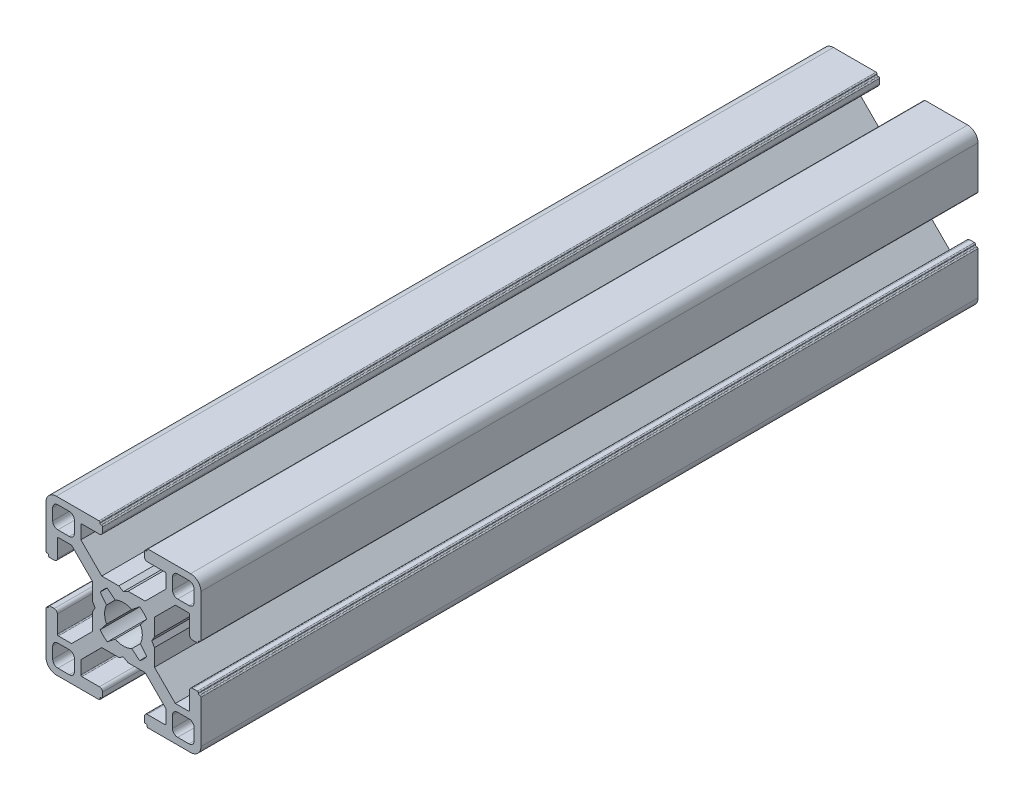
SolidWorks part; units mm, degrees
material "6061 Alloy"
ref_plane "Front" through (0, 0, 0) normal (0, 0, 1) x (1, 0, 0)
ref_plane "Top" through (0, 0, 0) normal (0, 1, 0) x (1, 0, 0)
ref_plane "Right" through (0, 0, 0) normal (1, 0, 0) x (0, 0, -1)
sketch "Sketch1" plane through (0, 0, 0) normal (0, 0, 1) x (1, 0, 0)
  line L0 (13.7, 12.7) -> (13.7, 10.5)
  line L1 (10.5, 9.5) -> (12.7, 9.5)
  line L2 (9.5, 12.7) -> (9.5, 10.5)
  line L3 (10.5, 13.7) -> (12.7, 13.7)
  line L4 (3.1359, 4.5184) -> (1.6001, 3.2806)
  line L5 (3.2806, 1.6001) -> (4.5053, 3.1547)
  line L6 (6.0045, 0.9) -> (5.4849, 0)
  line L7 (6.0045, 4.2045) -> (6.0045, 0.9)
  line L8 (0, -5.4849) -> (0.9, -6)
  line L9 (0.9, -6) -> (4.2045, -6)
  line L10 (4.2045, -6) -> (8.25, -10.05)
  line L11 (8.25, -10.05) -> (8.25, -12.6)
  line L12 (4.65, -12.8) -> (8.05, -12.8)
  line L13 (4.05, -14.3) -> (4.05, -13.4)
  line L14 (4.25, -14.5) -> (4.35, -14.5)
  line L15 (4.55, -14.8) -> (4.55, -14.7)
  line L16 (4.75, -15) -> (13, -15)
  line L17 (15, -13) -> (15, -4.75)
  line L18 (14.7, -4.55) -> (14.8, -4.55)
  line L19 (14.5, -4.35) -> (14.5, -4.25)
  line L20 (13.4, -4.05) -> (14.3, -4.05)
  line L21 (12.8, -8.05) -> (12.8, -4.65)
  line L22 (12.6, -8.25) -> (10.05, -8.25)
  line L23 (10.05, -8.25) -> (6.0045, -4.2045)
  line L24 (6.0045, -4.2045) -> (6.0045, -0.9)
  line L25 (6.0045, -0.9) -> (5.4849, 0)
  line L26 (10.05, 8.25) -> (6.0045, 4.2045)
  line L27 (12.6, 8.25) -> (10.05, 8.25)
  line L28 (12.8, 8.05) -> (12.8, 4.65)
  line L29 (13.4, 4.05) -> (14.3, 4.05)
  line L30 (14.5, 4.35) -> (14.5, 4.25)
  line L31 (14.7, 4.55) -> (14.8, 4.55)
  line L32 (15, 13) -> (15, 4.75)
  line L33 (4.75, 15) -> (13, 15)
  line L34 (4.55, 14.8) -> (4.55, 14.7)
  line L35 (4.25, 14.5) -> (4.35, 14.5)
  line L36 (4.05, 14.3) -> (4.05, 13.4)
  line L37 (4.65, 12.8) -> (8.05, 12.8)
  line L38 (8.25, 10.05) -> (8.25, 12.6)
  line L39 (4.2045, 6) -> (8.25, 10.05)
  line L40 (0.9, 6) -> (4.2045, 6)
  line L41 (0, 5.4849) -> (0.9, 6)
  line L42 (-13.7, -12.7) -> (-13.7, -10.5)
  line L43 (-10.5, -9.5) -> (-12.7, -9.5)
  line L44 (-9.5, -12.7) -> (-9.5, -10.5)
  line L45 (-10.5, -13.7) -> (-12.7, -13.7)
  line L46 (-3.1359, -4.5184) -> (-1.6001, -3.2806)
  line L47 (-3.2806, -1.6001) -> (-4.5053, -3.1547)
  line L48 (0, 5.4849) -> (-0.9, 6)
  line L49 (-0.9, 6) -> (-4.2045, 6)
  line L50 (-4.2045, 6) -> (-8.25, 10.05)
  line L51 (-8.25, 10.05) -> (-8.25, 12.6)
  line L52 (-4.65, 12.8) -> (-8.05, 12.8)
  line L53 (-4.05, 14.3) -> (-4.05, 13.4)
  line L54 (-4.25, 14.5) -> (-4.35, 14.5)
  line L55 (-4.55, 14.8) -> (-4.55, 14.7)
  line L56 (-4.75, 15) -> (-13, 15)
  line L57 (-15, 13) -> (-15, 4.75)
  line L58 (-14.7, 4.55) -> (-14.8, 4.55)
  line L59 (-14.5, 4.35) -> (-14.5, 4.25)
  line L60 (-13.4, 4.05) -> (-14.3, 4.05)
  line L61 (-12.8, 8.05) -> (-12.8, 4.65)
  line L62 (-12.6, 8.25) -> (-10.05, 8.25)
  line L63 (-10.05, 8.25) -> (-6.0045, 4.2045)
  line L64 (-6.0045, -0.9) -> (-5.4849, 0)
  line L65 (-6.0045, -4.2045) -> (-6.0045, -0.9)
  line L66 (-10.05, -8.25) -> (-6.0045, -4.2045)
  line L67 (-12.6, -8.25) -> (-10.05, -8.25)
  line L68 (-12.8, -8.05) -> (-12.8, -4.65)
  line L69 (-13.4, -4.05) -> (-14.3, -4.05)
  line L70 (-14.5, -4.35) -> (-14.5, -4.25)
  line L71 (-14.7, -4.55) -> (-14.8, -4.55)
  line L72 (-15, -13) -> (-15, -4.75)
  line L73 (-4.75, -15) -> (-13, -15)
  line L74 (-4.55, -14.8) -> (-4.55, -14.7)
  line L75 (-4.25, -14.5) -> (-4.35, -14.5)
  line L76 (-4.05, -14.3) -> (-4.05, -13.4)
  line L77 (3.2806, -1.6001) -> (4.5053, -3.1547)
  line L78 (3.1359, -4.5184) -> (1.6001, -3.2806)
  line L79 (-4.65, -12.8) -> (-8.05, -12.8)
  line L80 (-8.25, -10.05) -> (-8.25, -12.6)
  line L81 (-4.2045, -6) -> (-8.25, -10.05)
  line L82 (-0.9, -6) -> (-4.2045, -6)
  line L83 (0, -5.4849) -> (-0.9, -6)
  line L84 (10.5, -13.7) -> (12.7, -13.7)
  line L85 (9.5, -12.7) -> (9.5, -10.5)
  line L86 (10.5, -9.5) -> (12.7, -9.5)
  line L87 (13.7, -12.7) -> (13.7, -10.5)
  line L88 (-6.0045, 4.2045) -> (-6.0045, 0.9)
  line L89 (-6.0045, 0.9) -> (-5.4849, 0)
  line L90 (-3.2806, 1.6001) -> (-4.5053, 3.1547)
  line L91 (-3.1359, 4.5184) -> (-1.6001, 3.2806)
  line L92 (-10.5, 13.7) -> (-12.7, 13.7)
  line L93 (-9.5, 12.7) -> (-9.5, 10.5)
  line L94 (-10.5, 9.5) -> (-12.7, 9.5)
  line L95 (-13.7, 12.7) -> (-13.7, 10.5)
  line L96 (-23.4857, 0) -> (20.9308, 0) construction
  line L97 (0, 17.9563) -> (0, -17.361) construction
  arc A0 (13.7, 12.7) -> (12.7, 13.7) centre (12.7, 12.7) ccw
  arc A1 (12.7, 9.5) -> (13.7, 10.5) centre (12.7, 10.5) ccw
  arc A2 (9.5, 10.5) -> (10.5, 9.5) centre (10.5, 10.5) ccw
  arc A3 (10.5, 13.7) -> (9.5, 12.7) centre (10.5, 12.7) ccw
  arc A4 (1.6001, 3.2806) -> (-1.6001, 3.2806) centre (0, 0) ccw
  arc A5 (8.25, -12.6) -> (8.05, -12.8) centre (8.05, -12.6) cw
  arc A6 (4.65, -12.8) -> (4.05, -13.4) centre (4.65, -13.4) ccw
  arc A7 (4.05, -14.3) -> (4.25, -14.5) centre (4.25, -14.3) ccw
  arc A8 (4.35, -14.5) -> (4.55, -14.7) centre (4.35, -14.7) cw
  arc A9 (4.55, -14.8) -> (4.75, -15) centre (4.75, -14.8) ccw
  arc A10 (13, -15) -> (15, -13) centre (13, -13) ccw
  arc A11 (15, -4.75) -> (14.8, -4.55) centre (14.8, -4.75) ccw
  arc A12 (14.7, -4.55) -> (14.5, -4.35) centre (14.7, -4.35) cw
  arc A13 (14.5, -4.25) -> (14.3, -4.05) centre (14.3, -4.25) ccw
  arc A14 (13.4, -4.05) -> (12.8, -4.65) centre (13.4, -4.65) ccw
  arc A15 (12.8, -8.05) -> (12.6, -8.25) centre (12.6, -8.05) cw
  arc A16 (4.5053, 3.1547) -> (3.1359, 4.5184) centre (0, 0) ccw
  arc A17 (12.8, 8.05) -> (12.6, 8.25) centre (12.6, 8.05) ccw
  arc A18 (13.4, 4.05) -> (12.8, 4.65) centre (13.4, 4.65) cw
  arc A19 (14.5, 4.25) -> (14.3, 4.05) centre (14.3, 4.25) cw
  arc A20 (14.7, 4.55) -> (14.5, 4.35) centre (14.7, 4.35) ccw
  arc A21 (15, 4.75) -> (14.8, 4.55) centre (14.8, 4.75) cw
  arc A22 (13, 15) -> (15, 13) centre (13, 13) cw
  arc A23 (4.55, 14.8) -> (4.75, 15) centre (4.75, 14.8) cw
  arc A24 (4.35, 14.5) -> (4.55, 14.7) centre (4.35, 14.7) ccw
  arc A25 (4.05, 14.3) -> (4.25, 14.5) centre (4.25, 14.3) cw
  arc A26 (4.65, 12.8) -> (4.05, 13.4) centre (4.65, 13.4) cw
  arc A27 (8.25, 12.6) -> (8.05, 12.8) centre (8.05, 12.6) ccw
  arc A28 (-13.7, -12.7) -> (-12.7, -13.7) centre (-12.7, -12.7) ccw
  arc A29 (-12.7, -9.5) -> (-13.7, -10.5) centre (-12.7, -10.5) ccw
  arc A30 (-9.5, -10.5) -> (-10.5, -9.5) centre (-10.5, -10.5) ccw
  arc A31 (-10.5, -13.7) -> (-9.5, -12.7) centre (-10.5, -12.7) ccw
  arc A32 (-4.5053, -3.1547) -> (-3.1359, -4.5184) centre (0, 0) ccw
  arc A33 (-3.2806, 1.6001) -> (-3.2806, -1.6001) centre (0, 0) ccw
  arc A34 (-8.25, 12.6) -> (-8.05, 12.8) centre (-8.05, 12.6) cw
  arc A35 (-4.65, 12.8) -> (-4.05, 13.4) centre (-4.65, 13.4) ccw
  arc A36 (-4.05, 14.3) -> (-4.25, 14.5) centre (-4.25, 14.3) ccw
  arc A37 (-4.35, 14.5) -> (-4.55, 14.7) centre (-4.35, 14.7) cw
  arc A38 (-4.55, 14.8) -> (-4.75, 15) centre (-4.75, 14.8) ccw
  arc A39 (-13, 15) -> (-15, 13) centre (-13, 13) ccw
  arc A40 (-15, 4.75) -> (-14.8, 4.55) centre (-14.8, 4.75) ccw
  arc A41 (-14.7, 4.55) -> (-14.5, 4.35) centre (-14.7, 4.35) cw
  arc A42 (-14.5, 4.25) -> (-14.3, 4.05) centre (-14.3, 4.25) ccw
  arc A43 (-13.4, 4.05) -> (-12.8, 4.65) centre (-13.4, 4.65) ccw
  arc A44 (-12.8, 8.05) -> (-12.6, 8.25) centre (-12.6, 8.05) cw
  arc A45 (-4.5053, 3.1547) -> (-3.1359, 4.5184) centre (0, 0) cw
  arc A46 (-12.8, -8.05) -> (-12.6, -8.25) centre (-12.6, -8.05) ccw
  arc A47 (-13.4, -4.05) -> (-12.8, -4.65) centre (-13.4, -4.65) cw
  arc A48 (-14.5, -4.25) -> (-14.3, -4.05) centre (-14.3, -4.25) cw
  arc A49 (3.2806, 1.6001) -> (3.2806, -1.6001) centre (0, 0) cw
  arc A50 (4.5053, -3.1547) -> (3.1359, -4.5184) centre (0, 0) cw
  arc A51 (1.6001, -3.2806) -> (-1.6001, -3.2806) centre (0, 0) cw
  arc A52 (-14.7, -4.55) -> (-14.5, -4.35) centre (-14.7, -4.35) ccw
  arc A53 (-15, -4.75) -> (-14.8, -4.55) centre (-14.8, -4.75) cw
  arc A54 (-13, -15) -> (-15, -13) centre (-13, -13) cw
  arc A55 (-4.55, -14.8) -> (-4.75, -15) centre (-4.75, -14.8) cw
  arc A56 (10.5, -13.7) -> (9.5, -12.7) centre (10.5, -12.7) cw
  arc A57 (9.5, -10.5) -> (10.5, -9.5) centre (10.5, -10.5) cw
  arc A58 (12.7, -9.5) -> (13.7, -10.5) centre (12.7, -10.5) cw
  arc A59 (13.7, -12.7) -> (12.7, -13.7) centre (12.7, -12.7) cw
  arc A60 (-4.35, -14.5) -> (-4.55, -14.7) centre (-4.35, -14.7) ccw
  arc A61 (-4.05, -14.3) -> (-4.25, -14.5) centre (-4.25, -14.3) cw
  arc A62 (-4.65, -12.8) -> (-4.05, -13.4) centre (-4.65, -13.4) cw
  arc A63 (-8.25, -12.6) -> (-8.05, -12.8) centre (-8.05, -12.6) ccw
  arc A64 (-10.5, 13.7) -> (-9.5, 12.7) centre (-10.5, 12.7) cw
  arc A65 (-9.5, 10.5) -> (-10.5, 9.5) centre (-10.5, 10.5) cw
  arc A66 (-12.7, 9.5) -> (-13.7, 10.5) centre (-12.7, 10.5) cw
  arc A67 (-13.7, 12.7) -> (-12.7, 13.7) centre (-12.7, 12.7) cw
  point P81 (15, 15)
  point P82 (0, 15)
  point P203 (0, -15)
  point P204 (15, -15)
  point P206 (0, 0)
  point P207 (15, 0)
  point P219 (-15, 0)
  point P220 (-15, -15)
  point P221 (-15, 15)
extrude "Base-Extrude" add sketch "Sketch1" against normal blind 70
scale "Scale1" scale about origin uniform scaling no x scale factor 1 y scale factor 1 z scale factor 2.15
